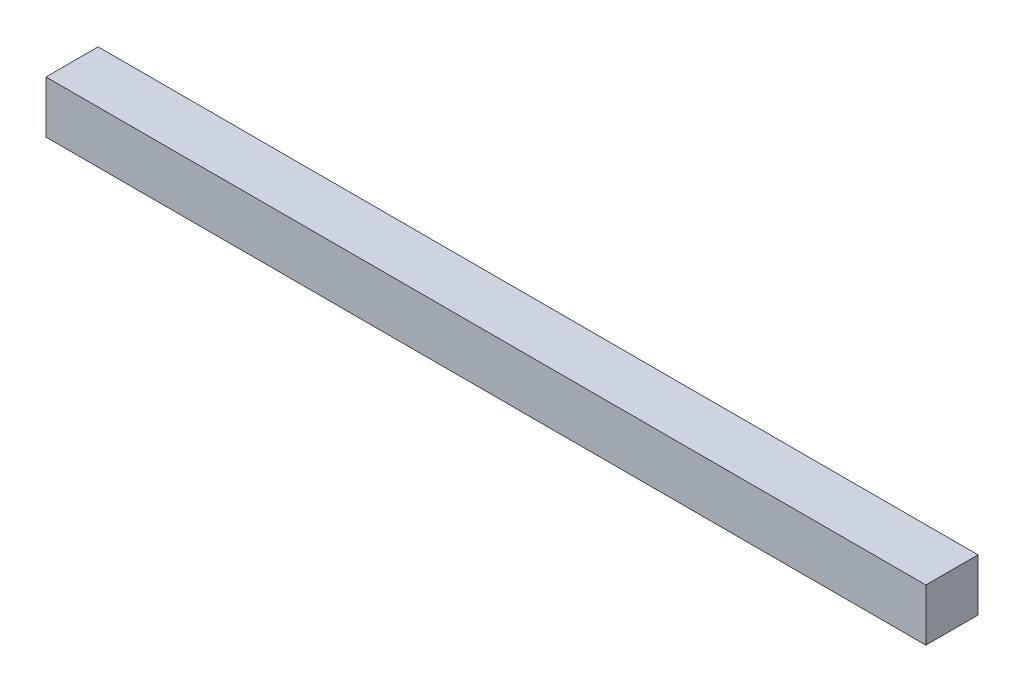
SolidWorks part; units mm, degrees
ref_plane "Front Plane" through (0, 0, 0) normal (0, 0, 1) x (1, 0, 0)
ref_plane "Top Plane" through (0, 0, 0) normal (0, 1, 0) x (1, 0, 0)
ref_plane "Right Plane" through (0, 0, 0) normal (1, 0, 0) x (0, 0, -1)
sketch "Sketch2" plane through (0, 0, 0) normal (1, 0, 0) x (0, 0, -1)
  line L1 (-0.32, -0.32) -> (0.32, -0.32)
  line L2 (-0.32, -0.32) -> (-0.32, 0.32)
  line L3 (-0.32, 0.32) -> (0.32, 0.32)
  line L4 (0.32, -0.32) -> (0.32, 0.32)
  line L5 (-0.32, -0.32) -> (0.32, 0.32) construction
  line L6 (-0.32, 0.32) -> (0.32, -0.32) construction
  point P0 (0, 0)
  dimension "D1" = 0.64
  dimension "D2" = 0.64
extrude "Boss-Extrude1" add sketch "Sketch2" along normal blind 10.8
